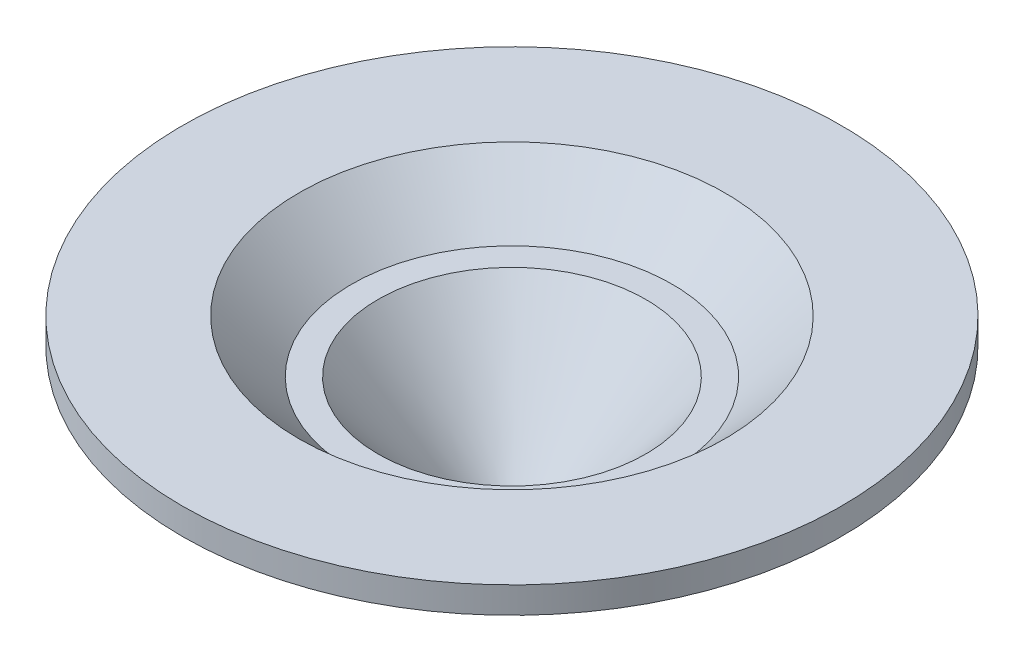
SolidWorks part; units mm, degrees
ref_plane "Front Plane" through (0, 0, 0) normal (0, 0, 1) x (1, 0, 0)
ref_plane "Top Plane" through (0, 0, 0) normal (0, 1, 0) x (1, 0, 0)
ref_plane "Right Plane" through (0, 0, 0) normal (1, 0, 0) x (0, 0, -1)
sketch "Sketch1" plane through (0, 0, 0) normal (1, 0, 0) x (0, 0, -1)
  line L0 (0, 0) -> (0, -1.6459) construction
  line L1 (1, -5) -> (5.0803, 0)
  line L2 (5.0803, 0) -> (6.0803, 0)
  line L3 (6.0803, 0) -> (8.0803, 2)
  line L4 (8.0803, 2) -> (12.5, 2)
  line L5 (12.5, 2) -> (12.5, 1)
  line L6 (12.5, 1) -> (10.5, 1)
  line L7 (10.5, 1) -> (8.5, -1)
  line L8 (8.5, -1) -> (6.5, -1)
  line L9 (6.5, -1) -> (2.5, -5)
  line L10 (2.5, -5) -> (1, -5)
  dimension "D1" = 5
  dimension "D2" = 12.5
  dimension "D3" = 1.5
  dimension "D4" = 3.5
  dimension "D5" = 5.0803
  dimension "D6" = 6.5
  dimension "D7" = 4
  dimension "D8" = 2
  dimension "D9" = 2
  dimension "D10" = 1
  dimension "D11" = 2
  dimension "D12" = 1
revolve "Revolve1" add sketch "Sketch1" angle 360 about L0
